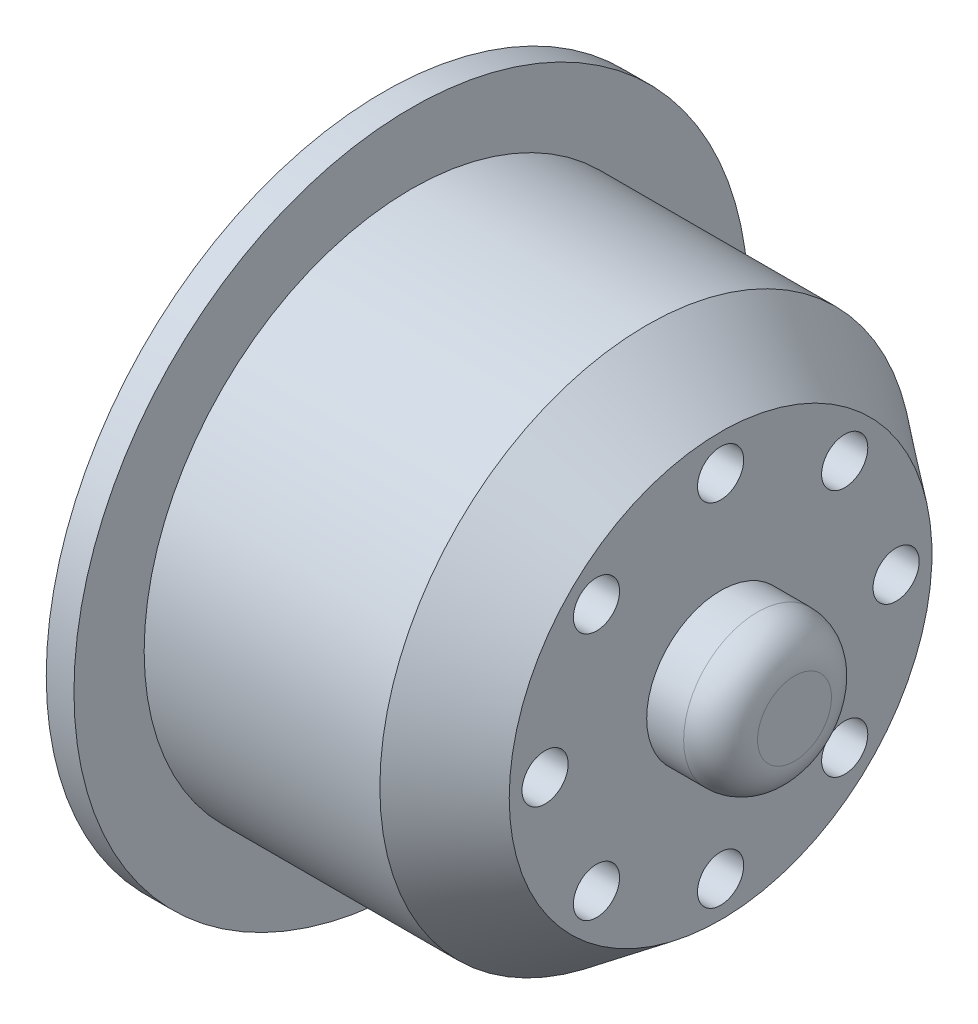
SolidWorks part; units mm, degrees
ref_plane "Front Plane" through (0, 0, 0) normal (0, 0, 1) x (1, 0, 0)
ref_plane "Top Plane" through (0, 0, 0) normal (0, 1, 0) x (1, 0, 0)
ref_plane "Right Plane" through (0, 0, 0) normal (1, 0, 0) x (0, 0, -1)
sketch "Sketch1" plane through (0, 0, 0) normal (0, 1, 0) x (1, 0, 0)
  line L0 (-12.3913, 0) -> (21, 0) construction
  line L1 (-6.1304, 14.45) -> (6.6264, 14.45)
  line L2 (6.6264, 14.45) -> (10.6196, 11.4409)
  line L5 (13.3727, 0) -> (-6.1304, 0)
  line L7 (10.6196, 11.4409) -> (10.6196, 4)
  line L8 (10.6196, 4) -> (14.6196, 4)
  line L9 (14.6196, 4) -> (14.6196, 0)
  line L10 (14.6196, 0) -> (13.3727, 0)
  line L11 (-6.1304, 14.45) -> (-6.1304, 18.25)
  line L12 (-6.1304, 18.25) -> (-7.6304, 18.25)
  line L13 (-7.6304, 18.25) -> (-7.6304, 0)
  line L14 (-7.6304, 0) -> (-6.1304, 0)
  dimension "D1" = 3.9932
  dimension "D2" = 143
  dimension "D3" = 127
  dimension "D4" = 5
  dimension "D5" = 28.9
  dimension "D6" = 16.75
  dimension "D7" = 4
  dimension "D8" = 8
  dimension "D9" = 3.8
  dimension "D10" = 1.5
revolve "Revolve1" add sketch "Sketch1" angle 360 about L0
sketch "Sketch2" plane through (10.6196, 0, 0) normal (1, 0, 0) x (0, 0, -1)
  circle A0 centre (0, 0) radius 9.5 construction
  circle A1 centre (0, 9.5) radius 1.25
  circle A3 centre (6.7175, 6.7175) radius 1.25
  circle A4 centre (9.5, 0) radius 1.25
  circle A5 centre (6.7175, -6.7175) radius 1.25
  circle A6 centre (0, -9.5) radius 1.25
  circle A7 centre (-6.7175, -6.7175) radius 1.25
  circle A8 centre (-9.5, 0) radius 1.25
  circle A9 centre (-6.7175, 6.7175) radius 1.25
  point P22 (0, 0)
  dimension "D1" = 19
  dimension "D2" = 2.5
  dimension "D3" = 8
extrude "Cut-Extrude1" cut sketch "Sketch2" against normal through all
fillet "Fillet1" radius 2 1 edges at (14.6196, 0, 4)
sketch "Sketch3" plane through (-7.6304, 0, 0) normal (-1, 0, 0) x (0, 0, 1)
  circle A0 centre (0, 0) radius 9.5 construction
  circle A1 centre (0, 9.5) radius 2.5
  circle A2 centre (6.7175, 6.7175) radius 2.5
  circle A3 centre (9.5, 0) radius 2.5
  circle A4 centre (6.7175, -6.7175) radius 2.5
  circle A5 centre (0, -9.5) radius 2.5
  circle A6 centre (-6.7175, -6.7175) radius 2.5
  circle A7 centre (-9.5, 0) radius 2.5
  circle A8 centre (-6.7175, 6.7175) radius 2.5
  point P23 (0, 0)
  dimension "D1" = 19
  dimension "D2" = 5
  dimension "D3" = 8
extrude "Cut-Extrude2" cut sketch "Sketch3" against normal offset from surface (13.25 mm away) 5 up to face at (10.6196, 9.5, -1.25)
sketch "Sketch4" plane through (-7.6304, 0, 0) normal (-1, 0, 0) x (0, 0, 1)
  circle A0 centre (0, 0) radius 4.65
  dimension "D1" = 9.3
extrude "Cut-Extrude3" cut sketch "Sketch4" against normal blind 10
